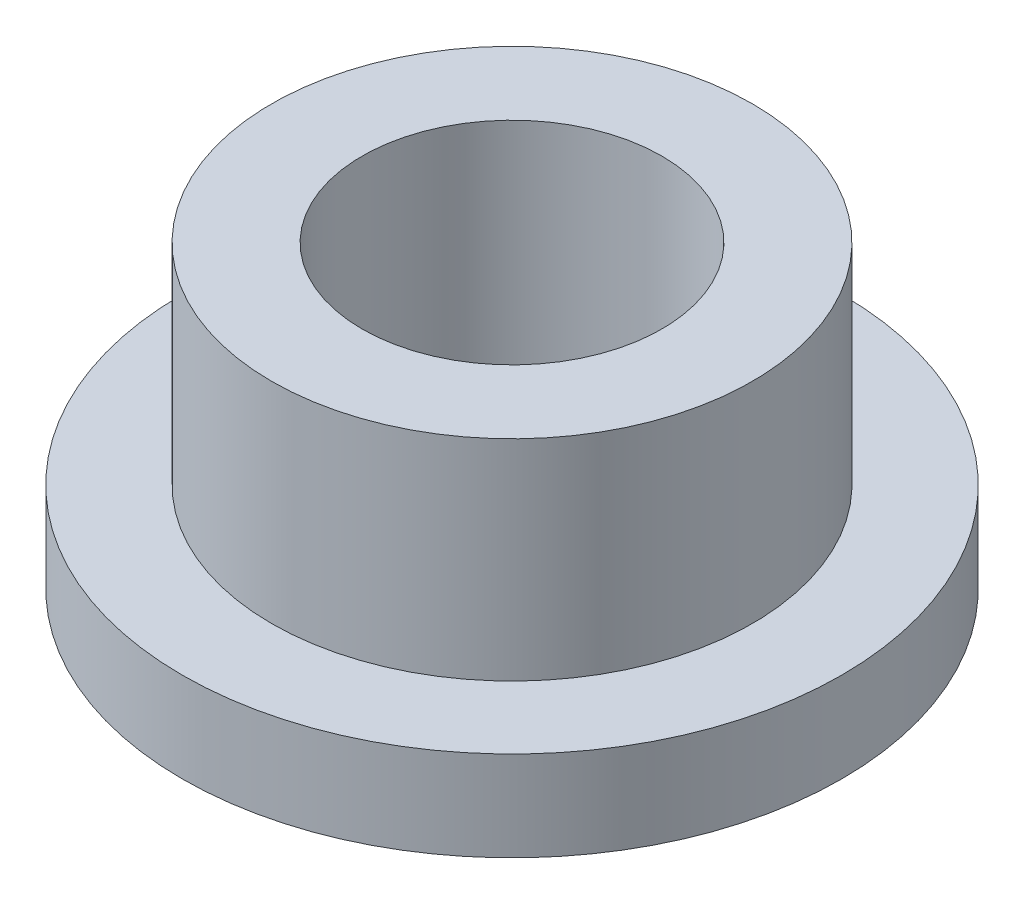
SolidWorks part; units mm, degrees
material "Manganese Bronze"
ref_plane "Front" through (0, 0, 0) normal (0, 0, 1) x (1, 0, 0)
ref_plane "Top" through (0, 0, 0) normal (0, 1, 0) x (1, 0, 0)
ref_plane "Right" through (0, 0, 0) normal (1, 0, 0) x (0, 0, -1)
sketch "Sketch1" plane through (0, 0, 0) normal (0, 1, 0) x (1, 0, 0)
  circle A0 centre (0, 0) radius 2.5
  circle A1 centre (0, 0) radius 4.01
  circle A2 centre (0, 0) radius 5.5
  dimension "ID" = 5
  dimension "OD" = 8.02
  dimension "FlangeOD" = 11
sketch "Sketch2" plane through (0, 0, 0) normal (0, 1, 0) x (1, 0, 0)
  circle A0 centre (0, 0) radius 2.5 construction
  circle A1 centre (0, 0) radius 4.01 construction
  circle A2 centre (0, 0) radius 2.5
  circle A3 centre (0, 0) radius 4.01
extrude "Boss-Extrude1" add sketch "Sketch2" along normal blind 5
sketch "Sketch3" plane through (0, 0, 0) normal (0, 1, 0) x (1, 0, 0)
  circle A0 centre (0, 0) radius 5.5 construction
  circle A1 centre (0, 0) radius 4.01 construction
  circle A2 centre (0, 0) radius 5.5
  circle A3 centre (0, 0) radius 4.01
extrude "Boss-Extrude2" add sketch "Sketch3" along normal blind 1.5
